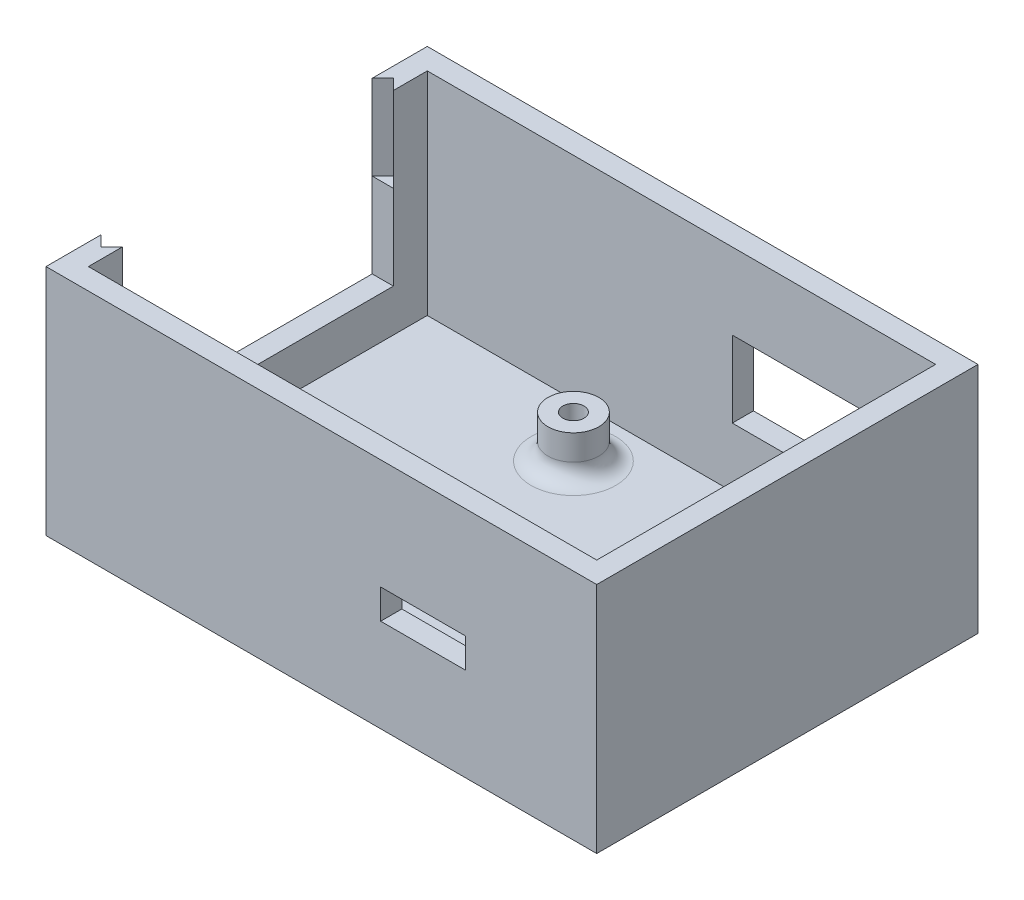
SolidWorks part; units mm, degrees
ref_plane "前视基准面" through (0, 0, 0) normal (0, 0, 1) x (1, 0, 0)
ref_plane "上视基准面" through (0, 0, 0) normal (0, 1, 0) x (1, 0, 0)
ref_plane "右视基准面" through (0, 0, 0) normal (1, 0, 0) x (0, 0, -1)
sketch "草图1" plane through (0, 0, 0) normal (0, 1, 0) x (1, 0, 0)
  line L1 (-32.5, 22.5) -> (32.5, 22.5)
  line L2 (-32.5, 22.5) -> (-32.5, -22.5)
  line L3 (-32.5, -22.5) -> (32.5, -22.5)
  line L4 (32.5, 22.5) -> (32.5, -22.5)
  line L5 (-32.5, 22.5) -> (32.5, -22.5) construction
  line L6 (-32.5, -22.5) -> (32.5, 22.5) construction
  point P0 (0, 0)
  dimension "D1" = 65
  dimension "D2" = 45
extrude "凸台-拉伸1" add sketch "草图1" along normal blind 27.5
shell "抽壳1" thickness 2.5
sketch "草图3" plane through (-30, 0, 0) normal (1, 0, 0) x (0, 0, -1)
  line L0 (20, 27.5) -> (-20, 27.5) construction
  line L1 (16, 27.5) -> (-16, 27.5)
  line L2 (16, 27.5) -> (16, 7.5)
  line L3 (16, 7.5) -> (-16, 7.5)
  line L4 (-16, 27.5) -> (-16, 7.5)
  line L5 (0, 27.5) -> (0, 7.5) construction
  line L6 (20, 2.5) -> (-20, 2.5) construction
  point P10 (0, 2.5)
  dimension "D1" = 32
  dimension "D2" = 5
extrude "切除-拉伸1" cut sketch "草图3" against normal through all
sketch "草图4" plane through (0, 27.5, 0) normal (0, 1, 0) x (1, 0, 0)
  line L0 (-32.5, 16) -> (-31.25, 17.25)
  line L1 (-31.25, 17.25) -> (-30, 16)
  line L2 (-32.5, 16) -> (-30, 16)
  line L3 (-32.5, -16) -> (-30, -16)
  line L4 (-30, 20) -> (-30, -20) construction
  line L5 (-32.5, -16) -> (-30, -16) construction
  line L6 (-30, -16) -> (-31.25, -17.25)
  line L7 (-31.25, -17.25) -> (-32.5, -16)
extrude "切除-拉伸2" cut sketch "草图4" against normal offset from surface (10 mm away) 10 up to face at (-31.25, 7.5, 0)
sketch "草图5" plane through (0, 2.5, 0) normal (0, 1, 0) x (1, 0, 0)
  line L0 (0, 0) -> (-37.9244, 0) construction
  line L1 (-32.5, -16) -> (-32.5, 16) construction
  circle A0 centre (-6.5, 13.75) radius 3
  circle A1 centre (-6.5, -13.75) radius 3
  circle A2 centre (-6.5, 13.75) radius 1.25
  circle A3 centre (-6.5, -13.75) radius 1.25
  dimension "D1" = 6
  dimension "D2" = 13.75
  dimension "D5" = 2.5
  dimension "D3" = 27.5
  dimension "D4" = 26
extrude "凸台-拉伸2" add sketch "草图5" along normal blind 5
sketch "草图6" plane through (0, 2.5, 0) normal (0, 1, 0) x (1, 0, 0)
  line L0 (30, -20) -> (30, 20) construction
  line L1 (30, 20) -> (-30, 20) construction
  circle A0 centre (20, -7) radius 3
  circle A1 centre (20, -7) radius 0.75
  dimension "D2" = 6
  dimension "D3" = 1.5
  dimension "D1" = 10
  dimension "D4" = 27
extrude "凸台-拉伸3" add sketch "草图6" along normal blind 5
sketch "草图7" plane through (0, 0, -20) normal (0, 0, 1) x (1, 0, 0)
  line L0 (30, 27.5) -> (30, 2.5) construction
  line L1 (28, 18.5) -> (6, 18.5)
  line L2 (28, 18.5) -> (28, 9.5)
  line L3 (28, 9.5) -> (6, 9.5)
  line L4 (6, 18.5) -> (6, 9.5)
  line L5 (30, 2.5) -> (-30, 2.5) construction
  dimension "D1" = 2
  dimension "D2" = 9
  dimension "D3" = 22
  dimension "D4" = 7
extrude "切除-拉伸3" cut sketch "草图7" against normal through all
sketch "草图8" plane through (0, 0, 20) normal (0, 0, -1) x (-1, 0, 0)
  line L0 (-30, 27.5) -> (-30, 2.5) construction
  line L1 (-7, 14.5) -> (-17, 14.5)
  line L2 (-7, 14.5) -> (-7, 11)
  line L3 (-7, 11) -> (-17, 11)
  line L4 (-17, 14.5) -> (-17, 11)
  line L5 (30, 2.5) -> (-30, 2.5) construction
  dimension "D1" = 13
  dimension "D2" = 10
  dimension "D3" = 3.5
  dimension "D4" = 8.5
extrude "切除-拉伸4" cut sketch "草图8" against normal through all
fillet "圆角1" radius 2 3 edges at (20, 2.5, 10) (-6.5, 2.5, 16.75) (-6.5, 2.5, -10.75)
